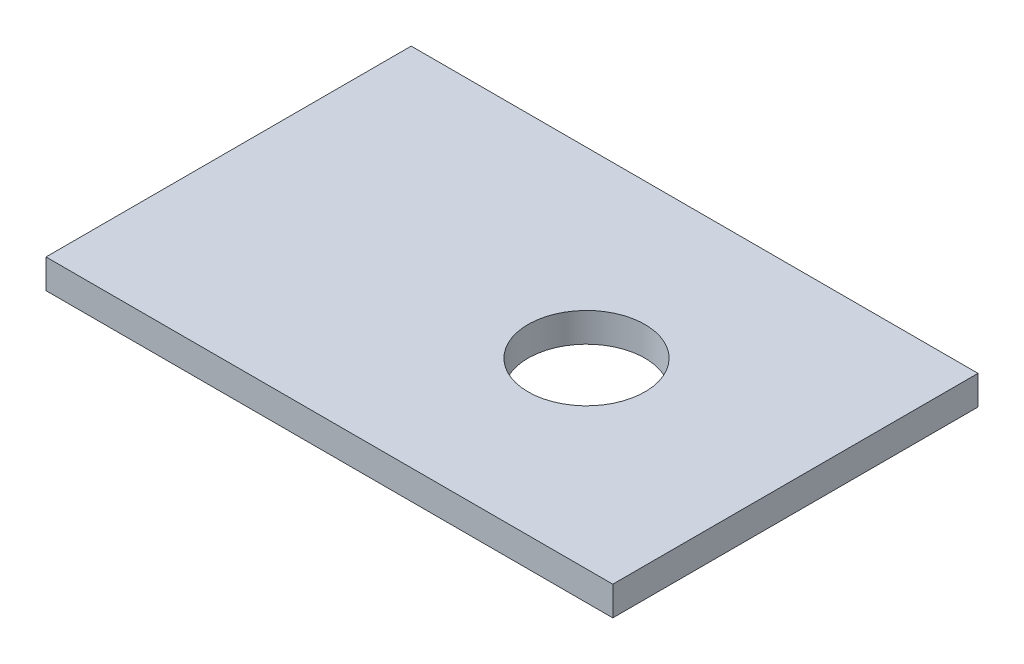
SolidWorks part; units mm, degrees
ref_plane "Front Plane" through (0, 0, 0) normal (0, 0, 1) x (1, 0, 0)
ref_plane "Top Plane" through (0, 0, 0) normal (0, 1, 0) x (1, 0, 0)
ref_plane "Right Plane" through (0, 0, 0) normal (1, 0, 0) x (0, 0, -1)
sketch "Sketch2" plane through (0, 0, 0) normal (0, 1, 0) x (1, 0, 0)
  line L1 (-19.4, -12.5) -> (19.4, -12.5)
  line L2 (-19.4, -12.5) -> (-19.4, 12.5)
  line L3 (-19.4, 12.5) -> (19.4, 12.5)
  line L4 (19.4, -12.5) -> (19.4, 12.5)
  line L5 (-19.4, -12.5) -> (19.4, 12.5) construction
  line L6 (-19.4, 12.5) -> (19.4, -12.5) construction
  point P0 (0, 0)
  dimension "D1" = 38.8
  dimension "D2" = 25
extrude "Boss-Extrude1" add sketch "Sketch2" along normal blind 2
sketch "Sketch3" plane through (0, 2, 0) normal (0, 1, 0) x (1, 0, 0)
  line L0 (-1.1, 0) -> (1.1, 0) construction
  line L1 (-19.4, 12.5) -> (-19.4, -12.5) construction
  circle A0 centre (5.1, 0) radius 4
  dimension "D2" = 8
  dimension "D1" = 24.5
extrude "Cut-Extrude1" cut sketch "Sketch3" against normal through all
